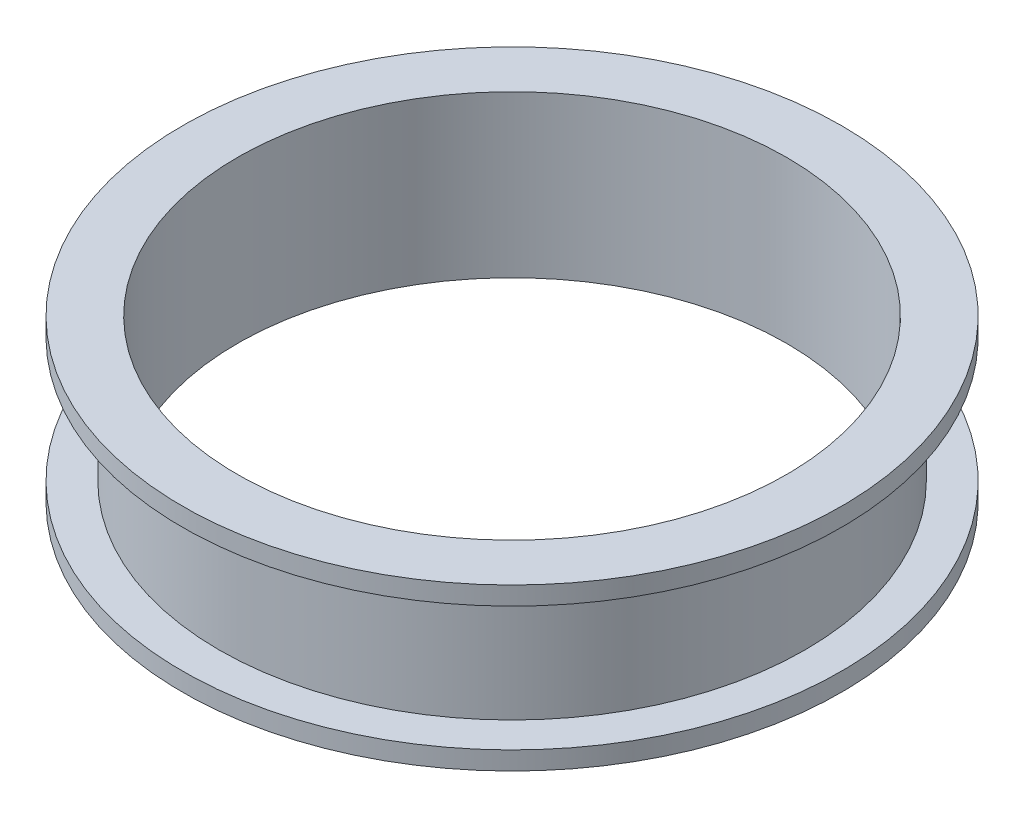
SolidWorks part; units mm, degrees
ref_plane "Front Plane" through (0, 0, 0) normal (0, 0, 1) x (1, 0, 0)
ref_plane "Top Plane" through (0, 0, 0) normal (0, 1, 0) x (1, 0, 0)
ref_plane "Right Plane" through (0, 0, 0) normal (1, 0, 0) x (0, 0, -1)
sketch "Sketch1" plane through (0, 0, 0) normal (0, 0, 1) x (1, 0, 0)
  line L0 (0, 0) -> (37.5, 0)
  line L1 (37.5, 0) -> (37.5, 19.5)
  line L2 (37.5, 19.5) -> (45, 19.5)
  line L3 (45, 19.5) -> (45, 17)
  line L4 (45, 17) -> (40, 17)
  line L5 (40, 17) -> (40, 0)
  line L6 (40, 0) -> (45, 0)
  line L7 (45, 0) -> (45, -2.5)
  line L8 (45, -2.5) -> (0, -2.5)
  line L9 (0, -2.5) -> (0, 0)
  dimension "D1" = 2.5
  dimension "D2" = 2.5
  dimension "D3" = 2.5
  dimension "D4" = 5
  dimension "D5" = 5
  dimension "D6" = 37.5
  dimension "D7" = 17
revolve "Revolve1" add sketch "Sketch1" angle 360 about L9
sketch "Sketch2" plane through (0, 0, 0) normal (0, 1, 0) x (1, 0, 0)
  circle A0 centre (0, 0) radius 37.5
  dimension "D1" = 75
extrude "Cut-Extrude1" cut sketch "Sketch2" against normal up to next
